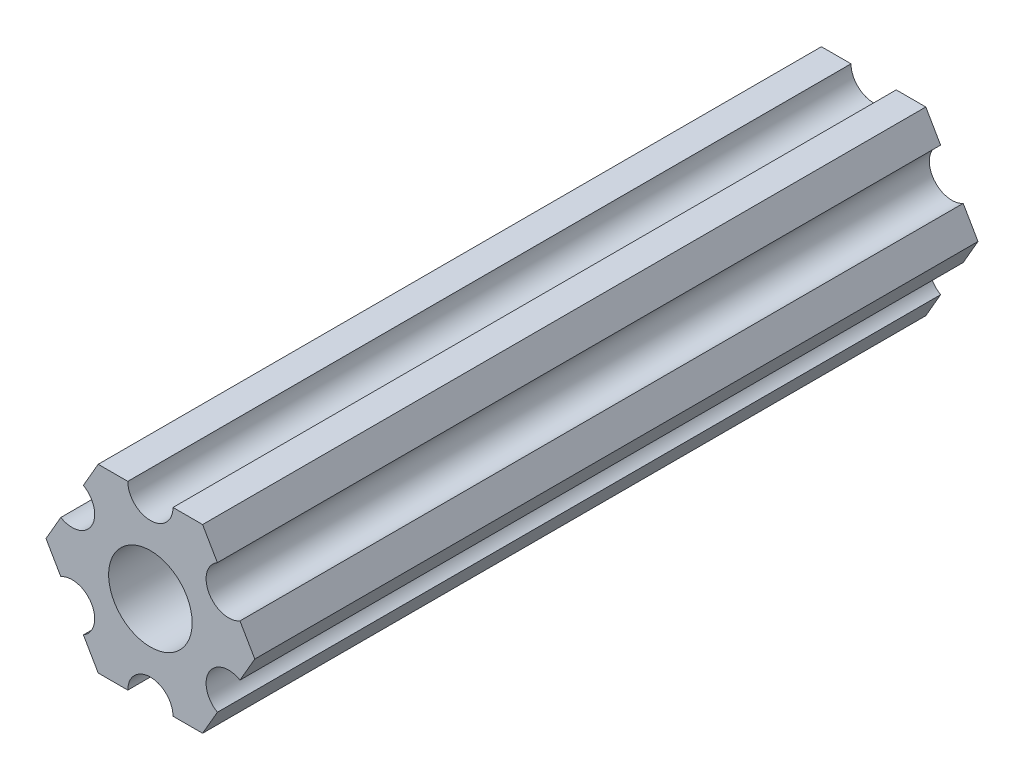
SolidWorks part; units mm, degrees
material "6061 Alloy"
ref_plane "Front Plane" through (0, 0, 0) normal (0, 0, 1) x (1, 0, 0)
ref_plane "Top Plane" through (0, 0, 0) normal (0, 1, 0) x (1, 0, 0)
ref_plane "Right Plane" through (0, 0, 0) normal (1, 0, 0) x (0, 0, -1)
ref_plane "Plane1" through (0, 0, 0) normal (0, 0, -1) x (-1, 0, 0)
sketch "Sketch1" plane through (0, 0, 0) normal (0, 0, -1) x (-1, 0, 0)
  line L0 (-4.7055, -4.5498) -> (-3.6662, -6.35)
  line L1 (-3.6662, -6.35) -> (-1.5875, -6.35)
  line L2 (1.5875, -6.35) -> (3.6662, -6.35)
  line L3 (3.6662, -6.35) -> (4.7055, -4.5498)
  line L4 (6.293, -1.8002) -> (7.3323, 0)
  line L5 (7.3323, 0) -> (6.293, 1.8002)
  line L6 (4.7055, 4.5498) -> (3.6662, 6.35)
  line L7 (3.6662, 6.35) -> (1.5875, 6.35)
  line L8 (-1.5875, 6.35) -> (-3.6662, 6.35)
  line L9 (-3.6662, 6.35) -> (-4.7055, 4.5498)
  line L10 (-6.293, 1.8002) -> (-7.3323, 0)
  line L11 (-7.3323, 0) -> (-6.293, -1.8002)
  circle A0 centre (0, 0) radius 2.9337
  arc A1 (-6.293, -1.8002) -> (-4.7055, -4.5498) centre (-5.4993, -3.175) cw
  arc A2 (-1.5875, -6.35) -> (1.5875, -6.35) centre (0, -6.35) cw
  arc A3 (4.7055, -4.5498) -> (6.293, -1.8002) centre (5.4993, -3.175) cw
  arc A4 (6.293, 1.8002) -> (4.7055, 4.5498) centre (5.4993, 3.175) cw
  arc A5 (1.5875, 6.35) -> (-1.5875, 6.35) centre (0, 6.35) cw
  arc A6 (-4.7055, 4.5498) -> (-6.293, 1.8002) centre (-5.4993, 3.175) cw
extrude "Boss-Extrude2" add sketch "Sketch1" along normal blind 50.8
